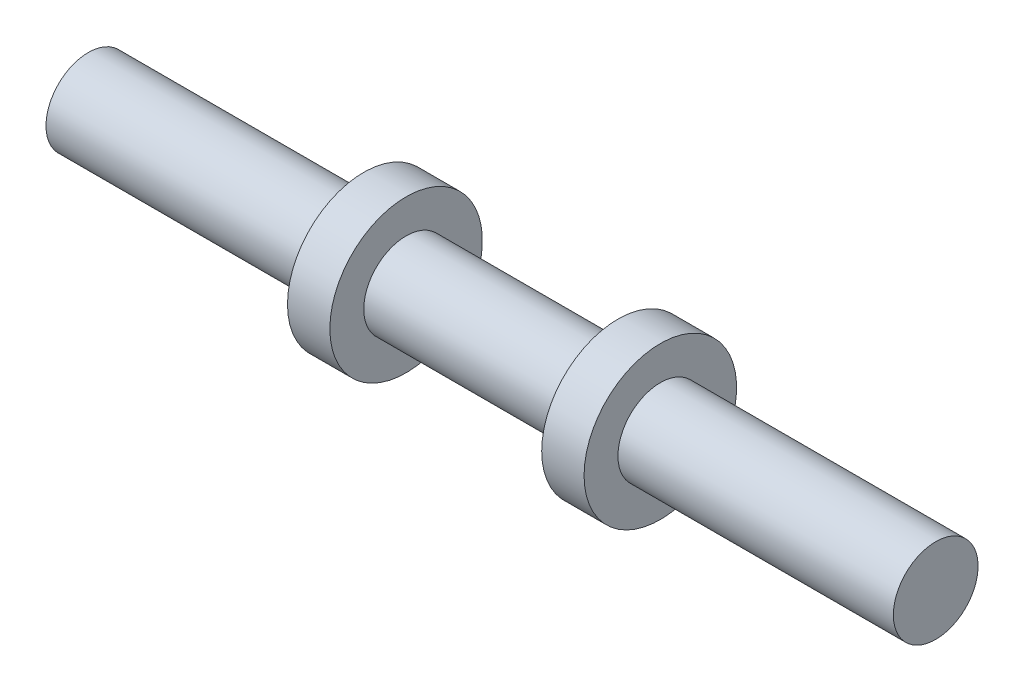
SolidWorks part; units mm, degrees
ref_plane "Front Plane" through (0, 0, 0) normal (0, 0, 1) x (1, 0, 0)
ref_plane "Top Plane" through (0, 0, 0) normal (0, 1, 0) x (1, 0, 0)
ref_plane "Right Plane" through (0, 0, 0) normal (1, 0, 0) x (0, 0, -1)
sketch "Sketch1" plane through (0, 0, 0) normal (1, 0, 0) x (0, 0, -1)
  circle A0 centre (0, 0) radius 1.8
extrude "Boss-Extrude1" add sketch "Sketch1" along normal blind 20
sketch "Sketch2" plane through (20, 0, 0) normal (1, 0, 0) x (0, 0, -1)
  line L0 (-1, 0) -> (-1.8, 0)
  line L1 (1, 0) -> (1.8, 0)
  arc A1 (-1, 0) -> (1, 0) centre (0, 0) cw
  circle A2 centre (0, 0) radius 1.8 construction
  arc A3 (-1.8, 0) -> (1.8, 0) centre (0, 0) cw
extrude "Cut-Extrude1" cut sketch "Sketch2" against normal blind 6.5 contours A1 L1 A3 L0
ref_plane "Plane1" through (12.5, 0, 0) normal (1, 0, 0) x (0, 0, -1)
sketch "Sketch3" plane through (12.5, 0, 0) normal (1, 0, 0) x (0, 0, -1)
  line L0 (-1, 0) -> (-1.8, 0)
  line L1 (1, 0) -> (1.8, 0)
  arc A0 (-1, 0) -> (1, 0) centre (0, 0) cw
  arc A1 (-1.8, 0) -> (1.8, 0) centre (0, 0) cw
extrude "Cut-Extrude2" cut sketch "Sketch3" against normal blind 5
ref_plane "Plane2" through (10, 0, 0) normal (1, 0, 0) x (0, 0, -1)
mirror "Mirror1" about plane through (10, 0, 0) normal (1, 0, 0) of "Cut-Extrude1"
mirror "Mirror2" about plane through (0, 0, 0) normal (0, 1, 0) of "Mirror1", "Cut-Extrude2", "Cut-Extrude1"
